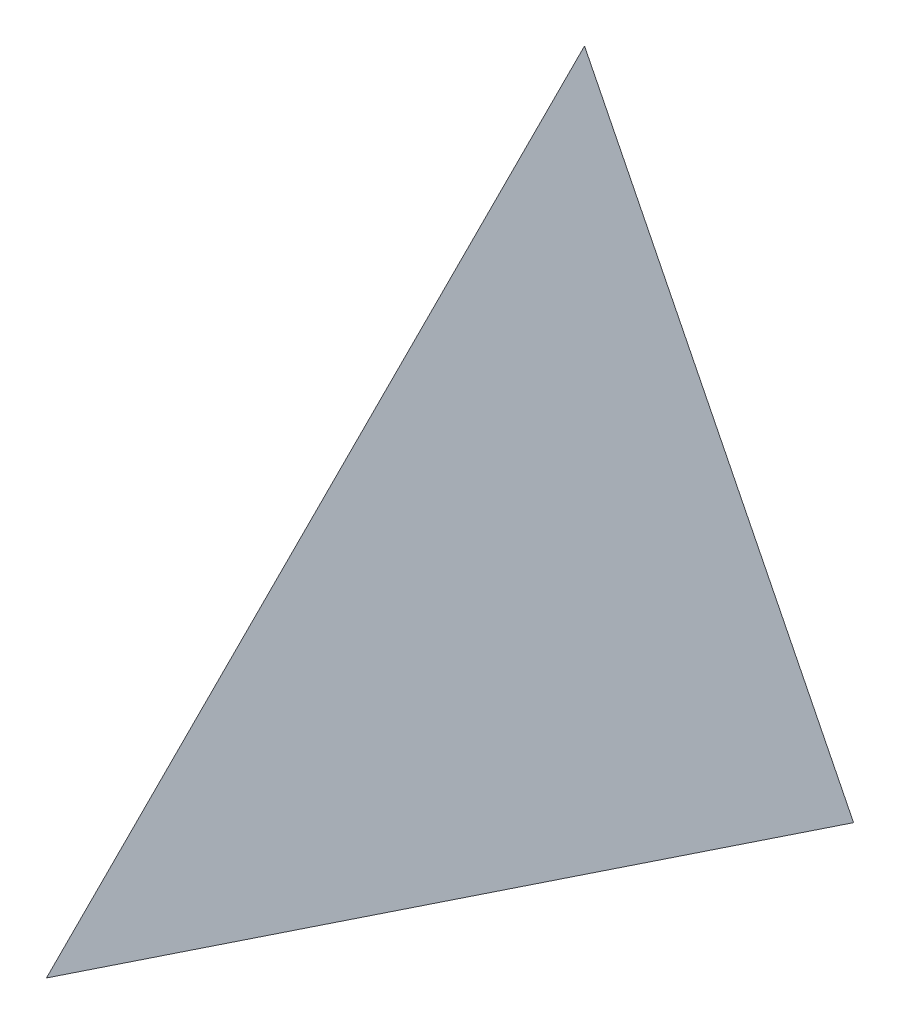
SolidWorks part; units mm, degrees
ref_plane "Front" through (0, 0, 0) normal (0, 0, 1) x (1, 0, 0)
ref_plane "Top" through (0, 0, 0) normal (0, 1, 0) x (1, 0, 0)
ref_plane "Right" through (0, 0, 0) normal (1, 0, 0) x (0, 0, -1)
sketch "Sketch1" plane through (0, 0, 0) normal (0, 1, 0) x (1, 0, 0)
  line L1 (-2, -2) -> (2, -2)
  line L2 (-2, -2) -> (-2, 2)
  line L3 (-2, 2) -> (2, 2)
  line L4 (2, -2) -> (2, 2)
  line L5 (-2, -2) -> (2, 2) construction
  line L6 (-2, 2) -> (2, -2) construction
  point P0 (0, 0)
  dimension "D1" = 4
  dimension "D2" = 4
extrude "Boss-Extrude1" add sketch "Sketch1" along normal blind 4
sketch3d "3DSketch1"
  line L0 (0, 4, -2) -> (-2, 0, -2)
  line L1 (2, 4, -2) -> (-2, 4, -2) construction
  line L2 (-2, 0, -2) -> (0, 0, 2)
  line L3 (-2, 0, 2) -> (2, 0, 2) construction
  line L4 (0, 0, 2) -> (0, 4, -2)
extrude "Cut-Extrude1" cut sketch "3DSketch1" along direction (0, -1, 0) on the side against the normal blind 10
sketch3d "3DSketch2"
  line L0 (0, 4, -2) -> (0, 0, 2)
  line L1 (0, 0, 2) -> (2, 0, -2)
  line L2 (2, 0, -2) -> (0, 4, -2)
extrude "Cut-Extrude2" cut sketch "3DSketch2" along direction (0, -1, 0) on the side of the normal blind 10
